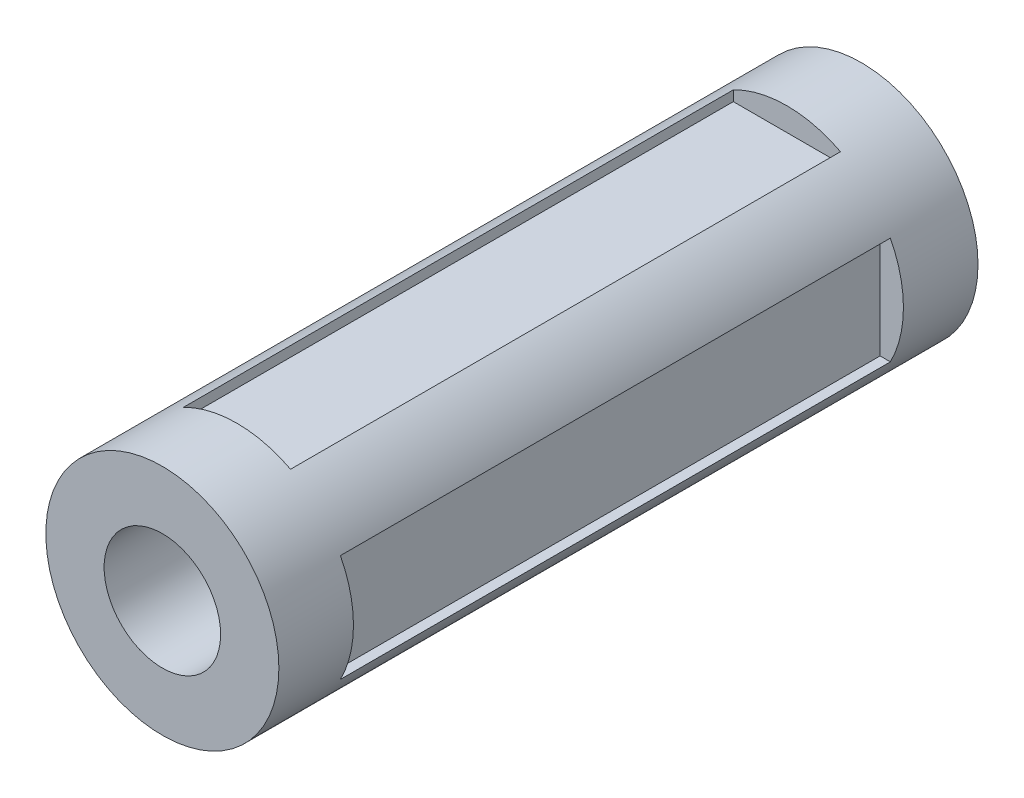
SolidWorks part; units mm, degrees
ref_plane "Front Plane" through (0, 0, 0) normal (0, 0, 1) x (1, 0, 0)
ref_plane "Top Plane" through (0, 0, 0) normal (0, 1, 0) x (1, 0, 0)
ref_plane "Right Plane" through (0, 0, 0) normal (1, 0, 0) x (0, 0, -1)
sketch "Sketch1" plane through (0, 0, 0) normal (0, 0, 1) x (1, 0, 0)
  circle A0 centre (0, 0) radius 50
  circle A1 centre (0, 0) radius 25
extrude "Boss-Extrude1" add sketch "Sketch1" along normal blind 300
ref_plane "Plane1" through (0, 50, 0) normal (0, 1, 0) x (1, 0, 0)
sketch "Sketch2" plane through (0, 50, 0) normal (0, 1, 0) x (1, 0, 0)
  line L2 (-24.996, -30) -> (24.996, -30)
  line L7 (-25, -270) -> (-24.996, -30)
  line L12 (-25, -270) -> (25, -270)
  line L17 (24.996, -30) -> (25, -270)
  line L18 (-23, -268) -> (-22.996, -32)
  line L19 (-22.996, -32) -> (22.996, -32)
  line L20 (22.996, -32) -> (23, -268)
  line L21 (-23, -268) -> (23, -268)
  point P7 (0, -30)
  point P11 (-24.998, -150)
  dimension "D1" = 240
  dimension "D2" = 2
extrude "Cut-Extrude1" cut sketch "Sketch2" against normal blind 10 contours L18 L19 L20 L21
pattern_circular "CirPattern1" count 4 over 360 about axis through (0, 0, 0) along (0, 0, 1) of "Cut-Extrude1"
